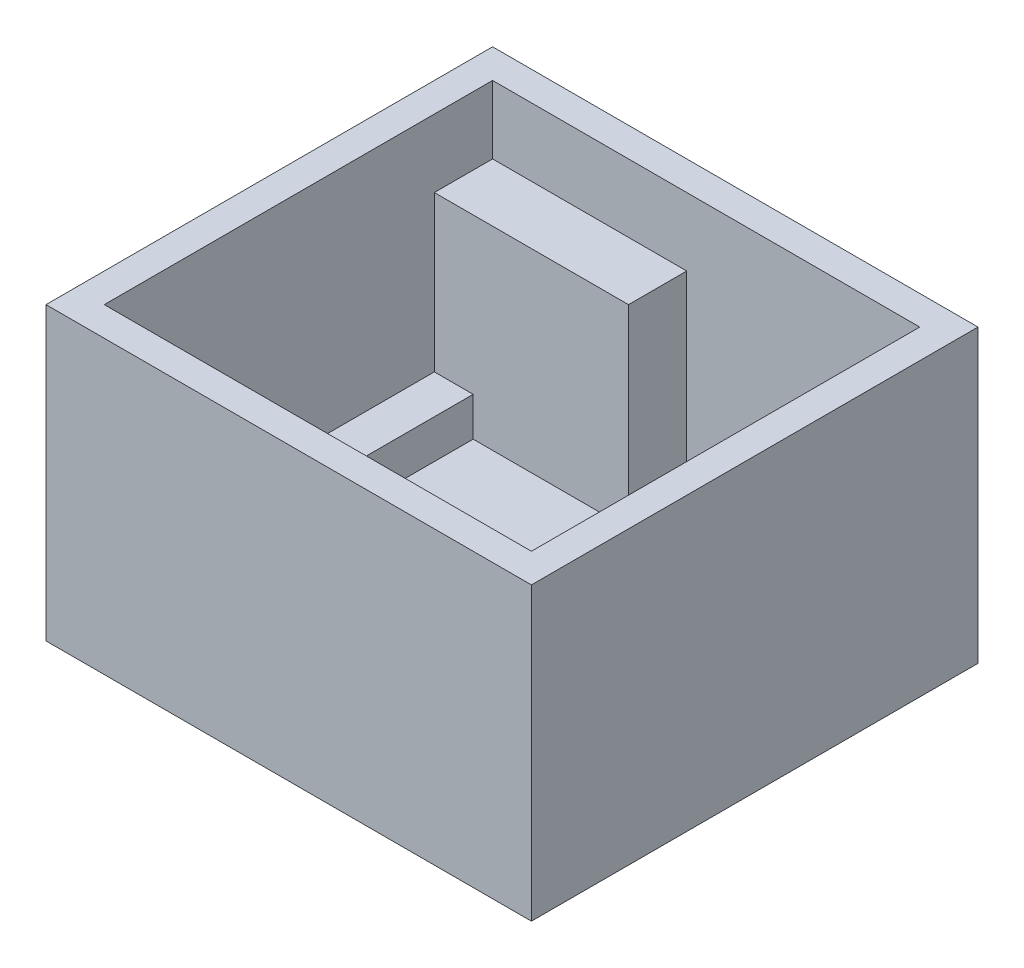
SolidWorks part; units mm, degrees
ref_plane "Front Plane" through (0, 0, 0) normal (0, 0, 1) x (1, 0, 0)
ref_plane "Top Plane" through (0, 0, 0) normal (0, 1, 0) x (1, 0, 0)
ref_plane "Right Plane" through (0, 0, 0) normal (1, 0, 0) x (0, 0, -1)
sketch "Sketch1" plane through (0, 0, 0) normal (0, 1, 0) x (1, 0, 0)
  line L0 (-12.5, 11.5) -> (12.5, 11.5)
  line L1 (-11, -10) -> (11, -10) construction
  line L2 (-11, -10) -> (-11, 10) construction
  line L3 (-11, 10) -> (11, 10) construction
  line L4 (11, -10) -> (11, 10) construction
  line L5 (-11, -10) -> (11, 10) construction
  line L6 (-11, 10) -> (11, -10) construction
  line L7 (12.5, -11.5) -> (12.5, 11.5)
  line L8 (-12.5, -11.5) -> (12.5, -11.5)
  line L9 (-12.5, -11.5) -> (-12.5, 11.5)
  point P0 (0, 0)
  dimension "D1" = 22
  dimension "D2" = 20
  dimension "D3" = 1.5
extrude "Boss-Extrude1" add sketch "Sketch1" along normal blind 15
shell "Shell1" thickness 1.5
sketch "Sketch3" plane through (0, 1.5, 0) normal (0, 1, 0) x (1, 0, 0)
  line L0 (0, 0) -> (0, 10) construction
  line L1 (-11, 10) -> (-9, 10)
  line L2 (-11, 10) -> (-11, 8)
  line L3 (-11, 8) -> (-9, 8)
  line L4 (-9, 10) -> (-9, 8)
  line L5 (11, 10) -> (-11, 10) construction
  line L6 (9, 10) -> (9, 8)
  line L7 (11, 8) -> (9, 8)
  line L8 (11, 10) -> (11, 8)
  line L9 (11, 10) -> (9, 10)
  line L10 (0, 0) -> (11, 0) construction
  line L11 (11, -10) -> (11, 10) construction
  line L12 (11, -10) -> (9, -10)
  line L13 (11, -10) -> (11, -8)
  line L14 (11, -8) -> (9, -8)
  line L15 (9, -10) -> (9, -8)
  line L16 (-9, -10) -> (-9, -8)
  line L17 (-11, -8) -> (-9, -8)
  line L18 (-11, -10) -> (-11, -8)
  line L19 (-11, -10) -> (-9, -10)
  dimension "D1" = 2
  dimension "D2" = 2
extrude "Boss-Extrude2" add sketch "Sketch3" along normal blind 2
sketch "Sketch2" plane through (0, 1.5, 0) normal (0, 1, 0) x (1, 0, 0)
  line L0 (-11, -7.25) -> (11, -7.25) construction
  line L1 (-11, 10) -> (-11, -10) construction
  line L2 (11, -10) -> (11, 10) construction
  line L3 (0, 0) -> (0, -7.25) construction
  line L4 (-11, -10) -> (11, -10) construction
  circle A0 centre (-8.2, -7.25) radius 1.75
  circle A1 centre (8.2, -7.25) radius 1.75
  point P11 (-6.45, -7.25)
  point P14 (-8.2, -9)
  dimension "D1" = 3.5
  dimension "D2" = 6.45
  dimension "D3" = 1
sketch "Sketch4" plane through (0, 1.5, 0) normal (0, 1, 0) x (1, 0, 0)
  line L0 (-11, 8) -> (-11, -8) construction
  line L1 (-9, 8) -> (-11, 8)
  line L2 (-9, 8) -> (-9, 1)
  line L3 (-9, 1) -> (-11, 1)
  line L4 (-11, 8) -> (-11, 1)
  line L5 (0, 0) -> (0, 10) construction
  line L6 (9, 10) -> (-9, 10) construction
  line L7 (11, 8) -> (11, 1)
  line L8 (9, 1) -> (11, 1)
  line L9 (9, 8) -> (9, 1)
  line L10 (9, 8) -> (11, 8)
  dimension "D1" = 7
extrude "Boss-Extrude3" add sketch "Sketch4" along normal up to surface (2 mm away) up to face at (-10, 3.5, -9)
sketch "Sketch5" plane through (0, 1.5, 0) normal (0, 1, 0) x (1, 0, 0)
  line L1 (-11, 10) -> (-1, 10)
  line L2 (-11, 10) -> (-11, 7)
  line L3 (-11, 7) -> (-1, 7)
  line L4 (-1, 10) -> (-1, 7)
  dimension "D1" = 3
  dimension "D2" = 10
extrude "Boss-Extrude4" add sketch "Sketch5" along normal blind 10
extrude "Boss-Extrude5" add sketch "Sketch2" along normal blind 2
sketch "Sketch6" plane through (0, 3.5, 0) normal (0, 1, 0) x (1, 0, 0)
  circle A0 centre (-8.2, -7.25) radius 1.25
  circle A1 centre (8.2, -7.25) radius 1.25
  dimension "D1" = 2.5
extrude "Boss-Extrude6" add sketch "Sketch6" along normal blind 4
